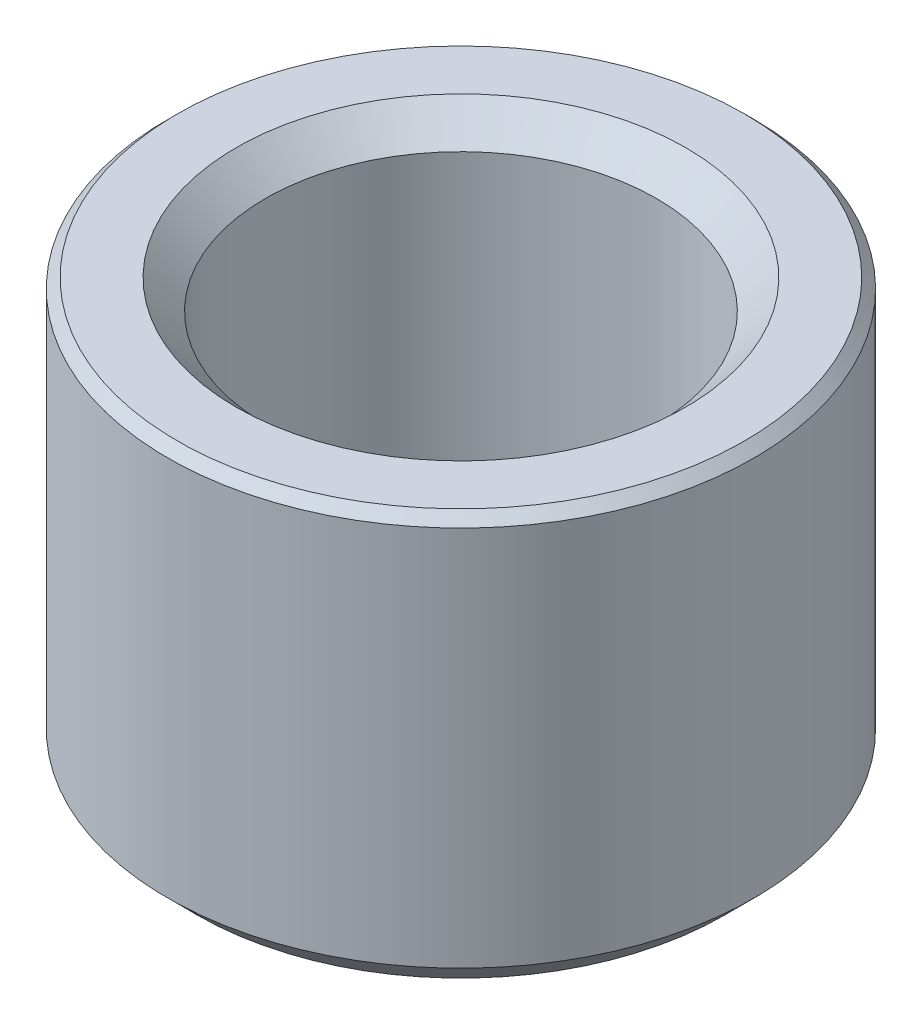
SolidWorks part; units mm, degrees
ref_plane "Front Plane" through (0, 0, 0) normal (0, 0, 1) x (1, 0, 0)
ref_plane "Top Plane" through (0, 0, 0) normal (0, 1, 0) x (1, 0, 0)
ref_plane "Right Plane" through (0, 0, 0) normal (1, 0, 0) x (0, 0, -1)
sketch "Sketch1" plane through (0, 0, 0) normal (0, 0, 1) x (1, 0, 0)
  line L0 (0, -0.7027) -> (0, 0.8905) construction
  line L1 (-1.35, 0) -> (-0.65, 0)
  line L2 (-0.65, 0) -> (-0.5, 0.15)
  line L3 (-0.5, 0.15) -> (-1, 0.4504)
  line L4 (-1, 0.4504) -> (-1, 2)
  line L5 (-1, 2) -> (-1.15, 2.15)
  line L6 (-1.15, 2.15) -> (-1.45, 2.15)
  line L7 (-1.5, 2.1) -> (-1.5, 0.15)
  line L8 (-1.5, 0.15) -> (-1.35, 0)
  line L9 (-0.5, 0.15) -> (0, 0.15) construction
  line L10 (-0.5, 0.15) -> (-0.5, 2.15) construction
  line L11 (-1, 2) -> (-1, 2.15) construction
  line L12 (-1, 0.507) -> (-0.95, 0.4204) construction
  line L13 (-1.45, 2.15) -> (-1.5, 2.1)
  dimension "D1" = 3
  dimension "D2" = 2
  dimension "D3" = 45
  dimension "D4" = 0.15
  dimension "D5" = 45
  dimension "D6" = 0.15
  dimension "D7" = 45
  dimension "D8" = 0.15
  dimension "D9" = 59
  dimension "D10" = 2
  dimension "D11" = 1
  dimension "D12" = 30
  dimension "D13" = 0.1
  dimension "D14" = 45
  dimension "D15" = 0.05
revolve "Revolve1" add sketch "Sketch1" angle 360 about L0
